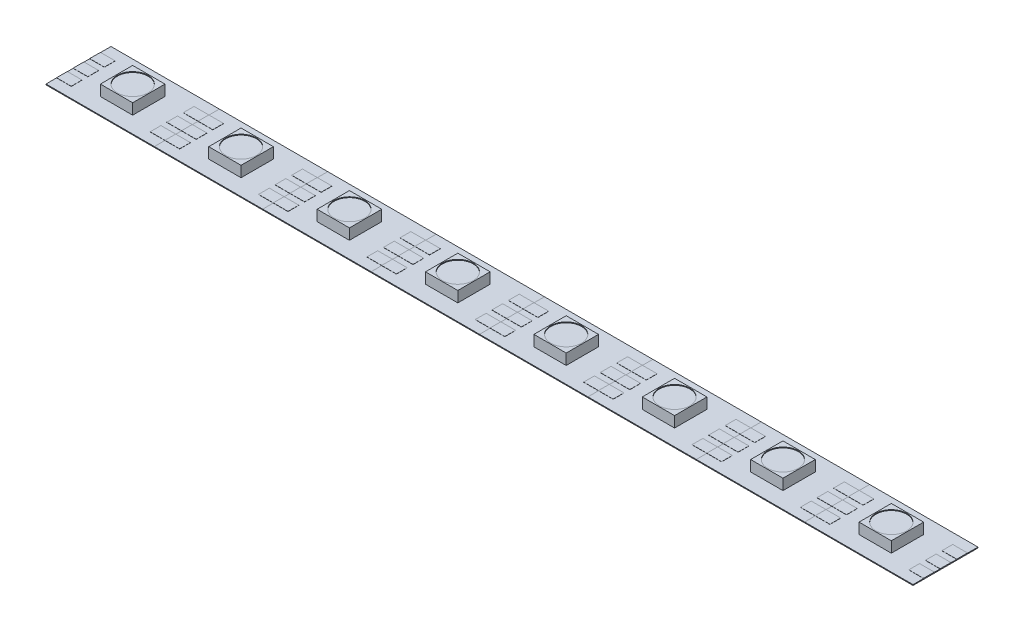
SolidWorks part; units mm, degrees
ref_plane "Front Plane" through (0, 0, 0) normal (0, 0, 1) x (1, 0, 0)
ref_plane "Top Plane" through (0, 0, 0) normal (0, 1, 0) x (1, 0, 0)
ref_plane "Right Plane" through (0, 0, 0) normal (1, 0, 0) x (0, 0, -1)
sketch "Sketch1" plane through (0, 0, 0) normal (0, 1, 0) x (1, 0, 0)
  line L0 (-8.3058, 4.9784) -> (8.3058, -4.9784) construction
  line L1 (-8.3058, 4.9784) -> (8.3058, 4.9784)
  line L2 (-8.3058, 4.9784) -> (-8.3058, -4.9784)
  line L3 (-8.3058, -4.9784) -> (8.3058, -4.9784)
  line L4 (8.3058, 4.9784) -> (8.3058, -4.9784)
  dimension "D1" = 9.9568
  dimension "D2" = 16.6116
extrude "Boss-Extrude1" add sketch "Sketch1" along normal blind 0.127
sketch "Sketch3" plane through (0, 0.127, 0) normal (0, 1, 0) x (1, 0, 0)
  line L0 (-8.3058, 4.9784) -> (8.3058, -4.9784) construction
  line L1 (-2.4765, 2.4765) -> (2.4765, -2.4765) construction
  line L2 (-2.4765, 2.4765) -> (2.4765, 2.4765)
  line L3 (-2.4765, 2.4765) -> (-2.4765, -2.4765)
  line L4 (-2.4765, -2.4765) -> (2.4765, -2.4765)
  line L5 (2.4765, 2.4765) -> (2.4765, -2.4765)
  dimension "D1" = 4.953
extrude "Boss-Extrude3" add sketch "Sketch3" along normal blind 1.651
sketch "Sketch4" plane through (0, 0.127, 0) normal (0, 1, 0) x (1, 0, 0)
  line L0 (-8.3058, 0) -> (8.3058, 0) construction
  line L1 (-8.3058, 4.9784) -> (-8.3058, -4.9784) construction
  line L2 (8.3058, -4.9784) -> (8.3058, 4.9784) construction
  line L3 (-6.047, 0) -> (-8.3058, 0) construction
  line L4 (-8.3058, 0.8255) -> (-6.047, 0.8255)
  line L5 (-8.3058, 0.8255) -> (-8.3058, -0.8255)
  line L6 (-8.3058, -0.8255) -> (-6.047, -0.8255)
  line L7 (-6.047, 0.8255) -> (-6.047, -0.8255)
  line L8 (-8.3058, 3.3655) -> (-6.047, 3.3655)
  line L9 (-6.047, 3.3655) -> (-6.047, 1.7145)
  line L10 (-8.3058, 1.7145) -> (-6.047, 1.7145)
  line L11 (-8.3058, 3.3655) -> (-8.3058, 1.7145)
  line L12 (-6.047, -3.3655) -> (-6.047, -1.7145)
  line L13 (-8.3058, -1.7145) -> (-6.047, -1.7145)
  line L14 (-8.3058, -3.3655) -> (-8.3058, -1.7145)
  line L15 (-8.3058, -3.3655) -> (-6.047, -3.3655)
  line L16 (0, 0) -> (0, -4.9784) construction
  line L17 (-8.3058, -4.9784) -> (8.3058, -4.9784) construction
  line L18 (8.3058, -3.3655) -> (8.3058, -1.7145)
  line L19 (8.3058, -3.3655) -> (6.047, -3.3655)
  line L20 (6.047, -3.3655) -> (6.047, -1.7145)
  line L21 (8.3058, -1.7145) -> (6.047, -1.7145)
  line L22 (8.3058, 0.8255) -> (8.3058, -0.8255)
  line L23 (8.3058, -0.8255) -> (6.047, -0.8255)
  line L24 (6.047, 0.8255) -> (6.047, -0.8255)
  line L25 (8.3058, 0.8255) -> (6.047, 0.8255)
  line L26 (8.3058, 1.7145) -> (6.047, 1.7145)
  line L27 (6.047, 3.3655) -> (6.047, 1.7145)
  line L28 (8.3058, 3.3655) -> (8.3058, 1.7145)
  line L29 (8.3058, 3.3655) -> (6.047, 3.3655)
  dimension "D1" = 1.651
  dimension "D2" = 2
extrude "Boss-Extrude4" add sketch "Sketch4" along normal blind 0.0254
sketch "Sketch5" plane through (0, 1.778, 0) normal (0, 1, 0) x (1, 0, 0)
  circle A0 centre (0, 0) radius 2.3483
extrude "Cut-Extrude1" cut sketch "Sketch5" against normal blind 0.127
pattern_linear "LPattern1" count 8 spacing 16.6116 along (1, 0, 0) of "Boss-Extrude3", "Boss-Extrude4", "Cut-Extrude1", "Boss-Extrude1"
